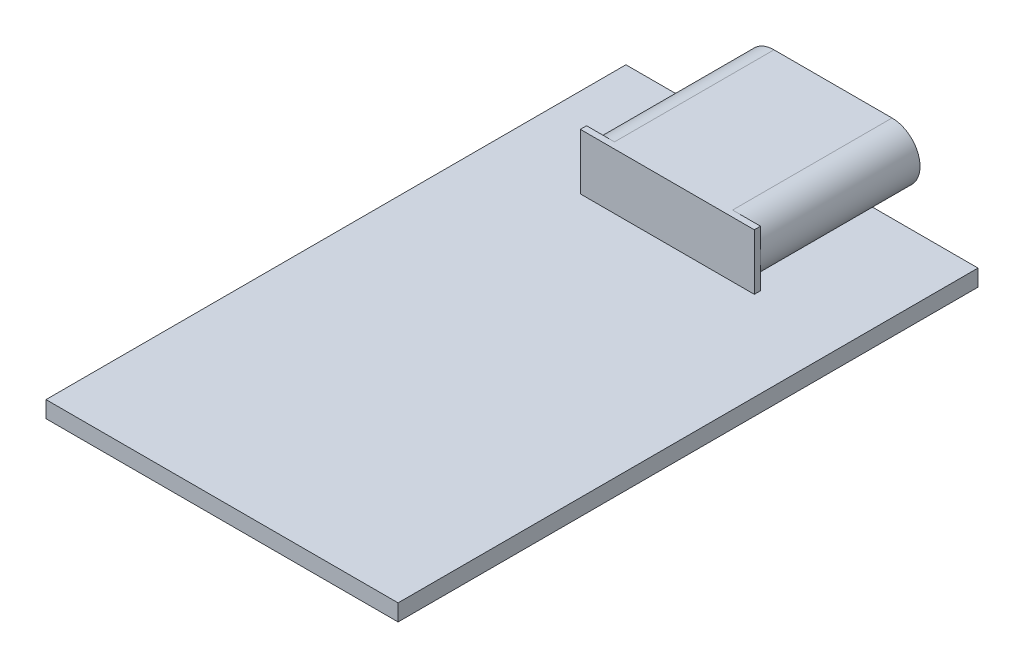
SolidWorks part; units mm, degrees
ref_plane "Front Plane" through (0, 0, 0) normal (0, 0, 1) x (1, 0, 0)
ref_plane "Top Plane" through (0, 0, 0) normal (0, 1, 0) x (1, 0, 0)
ref_plane "Right Plane" through (0, 0, 0) normal (1, 0, 0) x (0, 0, -1)
sketch "Sketch1" plane through (0, 0, 0) normal (0, 1, 0) x (1, 0, 0)
  line L1 (-8.5, -14) -> (8.5, -14)
  line L2 (-8.5, -14) -> (-8.5, 14)
  line L3 (-8.5, 14) -> (8.5, 14)
  line L4 (8.5, -14) -> (8.5, 14)
  line L5 (-8.5, -14) -> (8.5, 14) construction
  line L6 (-8.5, 14) -> (8.5, -14) construction
  point P0 (0, 0)
  dimension "D1" = 28
  dimension "D2" = 17
extrude "Boss-Extrude1" add sketch "Sketch1" along normal blind 0.8
sketch "Sketch3" plane through (0, 0.8, 0) normal (0, 1, 0) x (1, 0, 0)
  line L0 (0, 14) -> (0, -14) construction
  line L1 (8.5, 14) -> (-8.5, 14) construction
  line L2 (-8.5, -14) -> (8.5, -14) construction
  line L4 (-4.2, 15.5) -> (4.2, 15.5)
  line L5 (-4.2, 15.5) -> (-4.2, 7.5)
  line L6 (-4.2, 7.5) -> (4.2, 7.5)
  line L7 (4.2, 15.5) -> (4.2, 7.5)
  line L8 (-4.2, 15.5) -> (4.2, 7.5) construction
  line L9 (-4.2, 7.5) -> (4.2, 15.5) construction
  point P6 (0, 11.5)
  dimension "D1" = 1.5
  dimension "D2" = 8
  dimension "D3" = 8.4
extrude "Boss-Extrude2" add sketch "Sketch3" along normal blind 2.7
sketch "Sketch4" plane through (0, 0, -15.5) normal (0, 0, -1) x (-1, 0, 0)
  line L0 (0, 0.8) -> (0, 3.5) construction
  line L1 (-4.2, 0.8) -> (4.2, 0.8) construction
  line L2 (-4.2, 3.5) -> (4.2, 3.5) construction
  line L3 (-2.85, 2.15) -> (2.85, 2.15) construction
  line L4 (-2.85, 3.5) -> (2.85, 3.5)
  line L5 (-2.85, 0.8) -> (2.85, 0.8)
  line L6 (-4.2, 3.5) -> (-4.2, 0.8) construction
  line L7 (-2.85, 2.15) -> (2.85, 2.15) construction
  line L8 (-2.85, 2.5) -> (2.85, 2.5)
  line L9 (-2.85, 1.8) -> (2.85, 1.8)
  line L10 (-2.85, 2.15) -> (2.85, 2.15) construction
  line L11 (-2.85, 3.25) -> (2.85, 3.25)
  line L12 (-2.85, 1.05) -> (2.85, 1.05)
  arc A0 (-2.85, 3.5) -> (-2.85, 0.8) centre (-2.85, 2.15) ccw
  arc A1 (2.85, 0.8) -> (2.85, 3.5) centre (2.85, 2.15) ccw
  arc A2 (-2.85, 2.5) -> (-2.85, 1.8) centre (-2.85, 2.15) ccw
  arc A3 (2.85, 1.8) -> (2.85, 2.5) centre (2.85, 2.15) ccw
  arc A4 (-2.85, 3.25) -> (-2.85, 1.05) centre (-2.85, 2.15) ccw
  arc A5 (2.85, 1.05) -> (2.85, 3.25) centre (2.85, 2.15) ccw
  point P8 (0, 2.15)
  point P13 (4.2, 2.15)
  point P14 (0, 2.15)
  point P15 (-4.2, 2.15)
  point P24 (0, 2.15)
  point P31 (0, 0)
  line M5 (-4.2, 0.8) -> (4.2, 0.8)
  line M6 (4.2, 0.8) -> (4.2, 3.5)
  line M7 (4.2, 3.5) -> (-4.2, 3.5)
  line M8 (-4.2, 3.5) -> (-4.2, 0.8)
  dimension "D1" = 1
  dimension "D2" = 0.25
extrude "Cut-Extrude1" cut sketch "Sketch4" against normal blind 7.7 contours A0 M7 M8 | A0 M8 M5 | A1 M5 M6 | A1 M6 M7 | L12 A5 L11 A4 A3 L9 A2 L8
